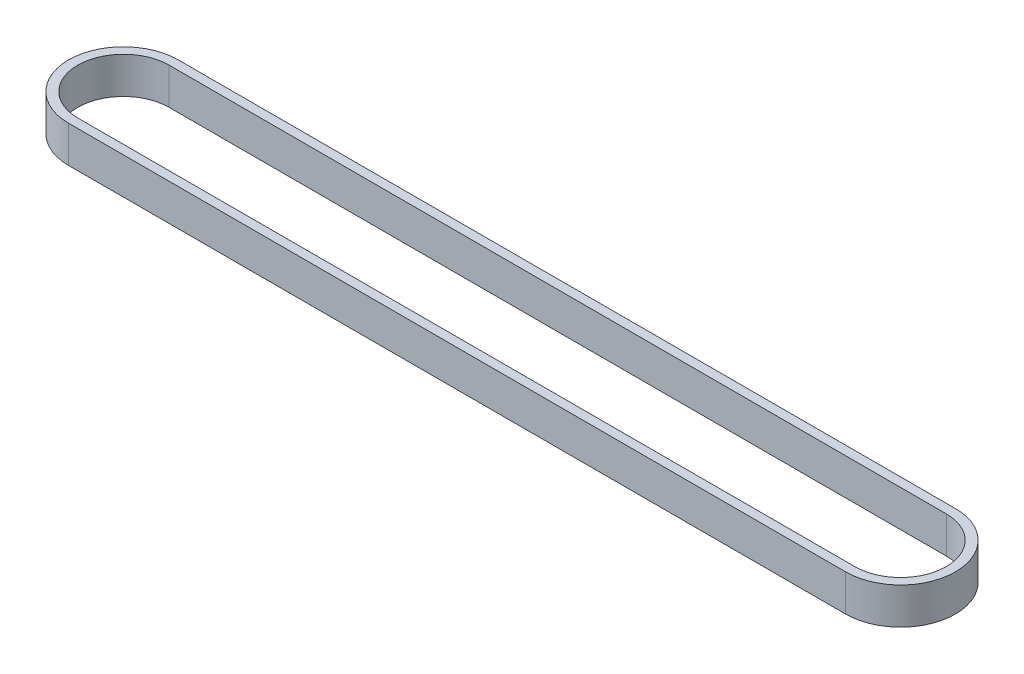
SolidWorks part; units mm, degrees
ref_plane "Front Plane" through (0, 0, 0) normal (0, 0, 1) x (1, 0, 0)
ref_plane "Top Plane" through (0, 0, 0) normal (0, 1, 0) x (1, 0, 0)
ref_plane "Right Plane" through (0, 0, 0) normal (1, 0, 0) x (0, 0, -1)
sketch "Sketch1" plane through (0, 0, 0) normal (0, 1, 0) x (1, 0, 0)
  line L0 (-399.0234, 41.021) -> (25.9766, 41.021)
  line L1 (-399.0234, 36.021) -> (25.9766, 36.021)
  line L3 (-399.0234, -13.979) -> (25.9766, -13.979)
  line L5 (-399.0234, -18.979) -> (25.9766, -18.979)
  arc A0 (-399.0234, 36.021) -> (-399.0234, -13.979) centre (-399.0234, 11.021) ccw
  arc A1 (25.9766, -13.979) -> (25.9766, 36.021) centre (25.9766, 11.021) ccw
  arc A2 (-399.0234, -18.979) -> (-399.0234, 41.021) centre (-399.0234, 11.021) cw
  arc A3 (25.9766, 41.021) -> (25.9766, -18.979) centre (25.9766, 11.021) cw
  dimension "D4" = 5
  dimension "D1" = 425
  dimension "D2" = 50
  dimension "D3" = 5
extrude "Boss-Extrude1" add sketch "Sketch1" along normal blind 20
